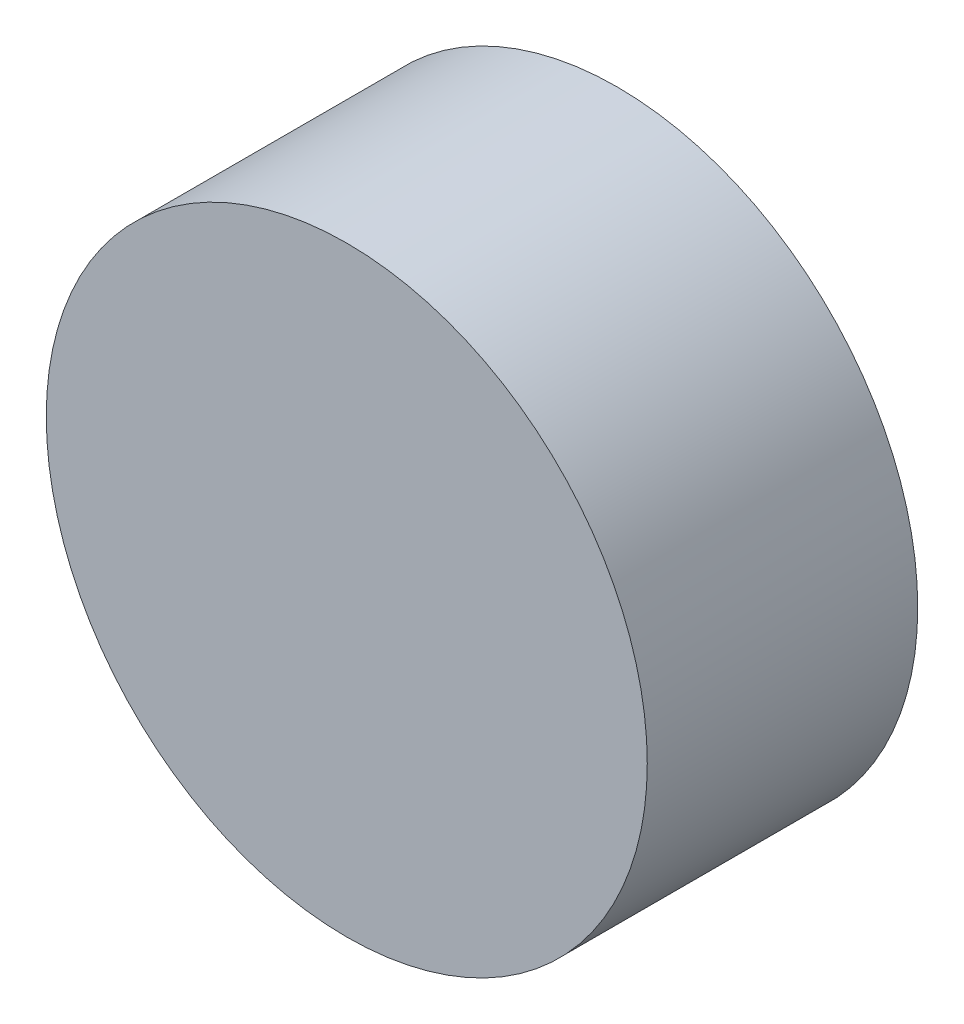
SolidWorks part; units mm, degrees
ref_plane "前视基准面" through (0, 0, 0) normal (0, 0, 1) x (1, 0, 0)
ref_plane "上视基准面" through (0, 0, 0) normal (0, 1, 0) x (1, 0, 0)
ref_plane "右视基准面" through (0, 0, 0) normal (1, 0, 0) x (0, 0, -1)
sketch "草图1" plane through (0, 0, 0) normal (0, 0, 1) x (1, 0, 0)
  circle A0 centre (0, 0) radius 20
  dimension "D1" = 40
extrude "凸台-拉伸1" add sketch "草图1" along normal blind 18
